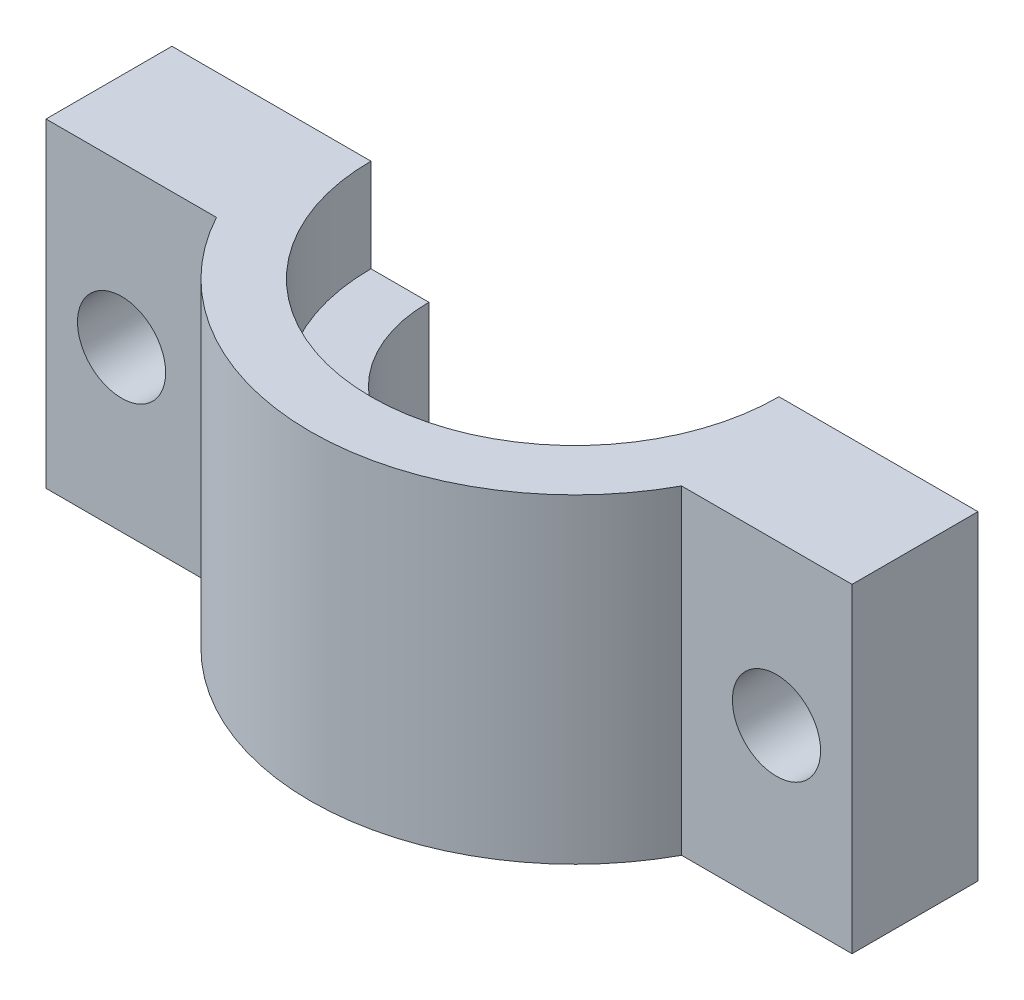
SolidWorks part; units mm, degrees
ref_plane "Front Plane" through (0, 0, 0) normal (0, 0, 1) x (1, 0, 0)
ref_plane "Top Plane" through (0, 0, 0) normal (0, 1, 0) x (1, 0, 0)
ref_plane "Right Plane" through (0, 0, 0) normal (1, 0, 0) x (0, 0, -1)
sketch "Sketch1" plane through (0, 0, 0) normal (0, 0, 1) x (1, 0, 0)
  line L1 (-16, 6.35) -> (16, 6.35)
  line L2 (-16, 6.35) -> (-16, -6.35)
  line L3 (-16, -6.35) -> (16, -6.35)
  line L4 (16, 6.35) -> (16, -6.35)
  line L5 (-16, 6.35) -> (16, -6.35) construction
  line L6 (-16, -6.35) -> (16, 6.35) construction
  point P0 (0, 0)
  dimension "D1" = 32
  dimension "D2" = 12.7
extrude "Boss-Extrude1" add sketch "Sketch1" along normal blind 12
sketch "Sketch3" plane through (0, 0, 0) normal (1, 0, 0) x (0, 0, -1)
  line L0 (0, 6.35) -> (-8.1, 6.35)
  line L1 (0, 6.35) -> (0, -6.35)
  line L2 (-12, 6.35) -> (0, 6.35) construction
  line L3 (-8.1, 6.35) -> (-8.1, 2.65)
  line L4 (-8.1, 2.65) -> (-5.8, 2.65)
  line L5 (-5.8, 2.65) -> (-5.8, -3.35)
  line L6 (-5.8, -3.35) -> (-8.1, -3.35)
  line L7 (-8.1, -3.35) -> (-8.1, -6.35)
  line L8 (-8.1, -6.35) -> (0, -6.35)
  line L9 (-12, -6.35) -> (0, -6.35) construction
  line L11 (0, -6.35) -> (0, 6.35) construction
  dimension "D1" = 8.1
  dimension "D2" = 5.8
  dimension "D3" = 3.7
  dimension "D4" = 3
revolve "Cut-Revolve1" cut sketch "Sketch3" angle 360 about L1
sketch "Sketch4" plane through (0, 6.35, 0) normal (0, 1, 0) x (1, 0, 0)
  line L0 (-16, -5) -> (-9.2331, -5)
  line L1 (-16, -12) -> (-16, 0) construction
  line L2 (9.2331, -5) -> (16, -5)
  line L3 (16, -12) -> (16, 0) construction
  line L7 (-16, -5) -> (-16, -15)
  line L8 (-16, -15) -> (16, -15)
  line L9 (16, -15) -> (16, -5)
  line L10 (-8.1, 0) -> (-16, 0) construction
  line L11 (16, -12) -> (-16, -12) construction
  arc A0 (-9.2331, -5) -> (9.2331, -5) centre (0, 0) ccw
  dimension "D1" = 21
  dimension "D2" = 5
  dimension "D3" = 3
extrude "Cut-Extrude1" cut sketch "Sketch4" against normal through all
sketch "Sketch5" plane through (0, 0, 5) normal (0, 0, 1) x (1, 0, 0)
  line L0 (-16, 0) -> (-10, 0) construction
  line L1 (-16, -6.35) -> (-16, 6.35) construction
  line L2 (16, 0) -> (10, 0) construction
  line L3 (16, -6.35) -> (16, 6.35) construction
  circle A0 centre (-13, 0) radius 1.75
  circle A1 centre (13, 0) radius 1.75
  dimension "D3" = 3.5
  dimension "D4" = 3.5
  dimension "D1" = 6
  dimension "D2" = 6
extrude "Cut-Extrude2" cut sketch "Sketch5" against normal through all
